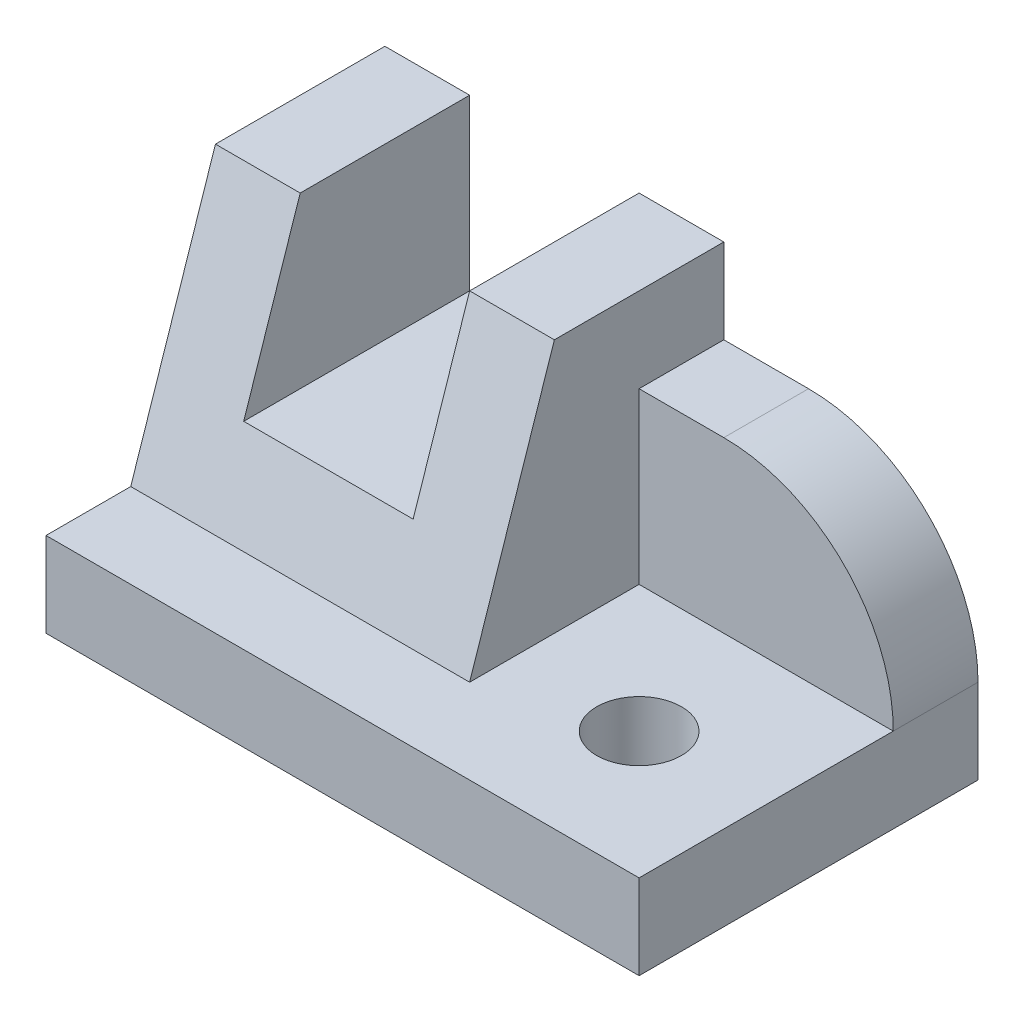
SolidWorks part; units mm, degrees
ref_plane "Front Plane" through (0, 0, 0) normal (0, 0, 1) x (1, 0, 0)
ref_plane "Top Plane" through (0, 0, 0) normal (0, 1, 0) x (1, 0, 0)
ref_plane "Right Plane" through (0, 0, 0) normal (1, 0, 0) x (0, 0, -1)
ref_plane "Plane1" through (0, 0, 0) normal (-1, 0, 0) x (0, -1, 0)
sketch "Sketch1" plane through (0, 0, 0) normal (-1, 0, 0) x (0, -1, 0)
  line L0 (-10, -10) -> (-40, -20)
  line L1 (-40, -20) -> (-10, -20)
  line L2 (-10, -20) -> (-10, -10)
  dimension "D1" = 30
  dimension "Width" = 10
extrude "Boss-Extrude1" add sketch "Sketch1" against normal blind 40
sketch "Sketch2" plane through (0, 0, -20) normal (0, 0, -1) x (-1, 0, 0)
  line L0 (-40, 40) -> (0, 40)
  line L1 (0, 40) -> (0, 10)
  line L2 (0, 10) -> (-40, 10)
  line L3 (-40, 10) -> (-40, 40)
extrude "Boss-Extrude2" add sketch "Sketch2" along normal blind 20
sketch "Sketch3" plane through (40, 0, 0) normal (1, 0, 0) x (0, 0, -1)
  line L0 (40, 10) -> (0, 10)
  line L1 (0, 10) -> (20, 40)
  line L2 (20, 40) -> (40, 40)
  line L3 (40, 40) -> (40, 10)
extrude "Boss-Extrude3" add sketch "Sketch3" along normal blind 30
sketch "Sketch4" plane through (70, 0, 0) normal (1, 0, 0) x (0, 0, -1)
  line L0 (20, 40) -> (0, 10)
  line L1 (0, 10) -> (30, 10)
  line L2 (30, 10) -> (30, 30)
  line L3 (30, 30) -> (40, 30)
  line L4 (40, 30) -> (40, 40)
  line L5 (40, 40) -> (20, 40)
extrude "Cut-Extrude1" cut sketch "Sketch4" against normal blind 30
sketch "Sketch5" plane through (0, 10, 0) normal (0, -1, 0) x (1, 0, 0)
  line L0 (70, 0) -> (70, -40)
  line L1 (70, -40) -> (0, -40)
  line L2 (0, -40) -> (0, 0)
  line L3 (0, 0) -> (70, 0)
extrude "Boss-Extrude4" add sketch "Sketch5" along normal blind 10
sketch "Sketch6" plane through (0, 0, -40) normal (0, 0, -1) x (-1, 0, 0)
  line L0 (-30, 40) -> (-30, 20)
  line L1 (-30, 20) -> (-10, 20)
  line L2 (-10, 20) -> (-10, 40)
  line L3 (-10, 40) -> (-30, 40)
extrude "Cut-Extrude2" cut sketch "Sketch6" against normal through all
hole_wizard "Ø10.0 (10) Diameter Hole1" positions "Sketch8" profile "Sketch7" hole size "Ø10.0" standard "ANSI Metric"
sketch "Sketch8" plane through (0, 0, 0) normal (0, -1, 0) x (-1, 0, 0)
  point P0 (-55, 15)
sketch "Sketch7" plane through (55, 0, -15) normal (1, 0, 0) x (0, 0, -1)
  line L0 (0, 0) -> (0, 40)
  line L1 (0, 40) -> (5, 40)
  line L2 (5, 40) -> (5, 0)
  line L5 (5, 0) -> (0, 0)
  line L11 (0, -6.35) -> (0, 107.95) construction
  dimension "Thru Hole Dia." = 10
  dimension "Thru Hole Depth" = 40
fillet "Fillet1" radius 20 1 edges at (70, 30, -35)
